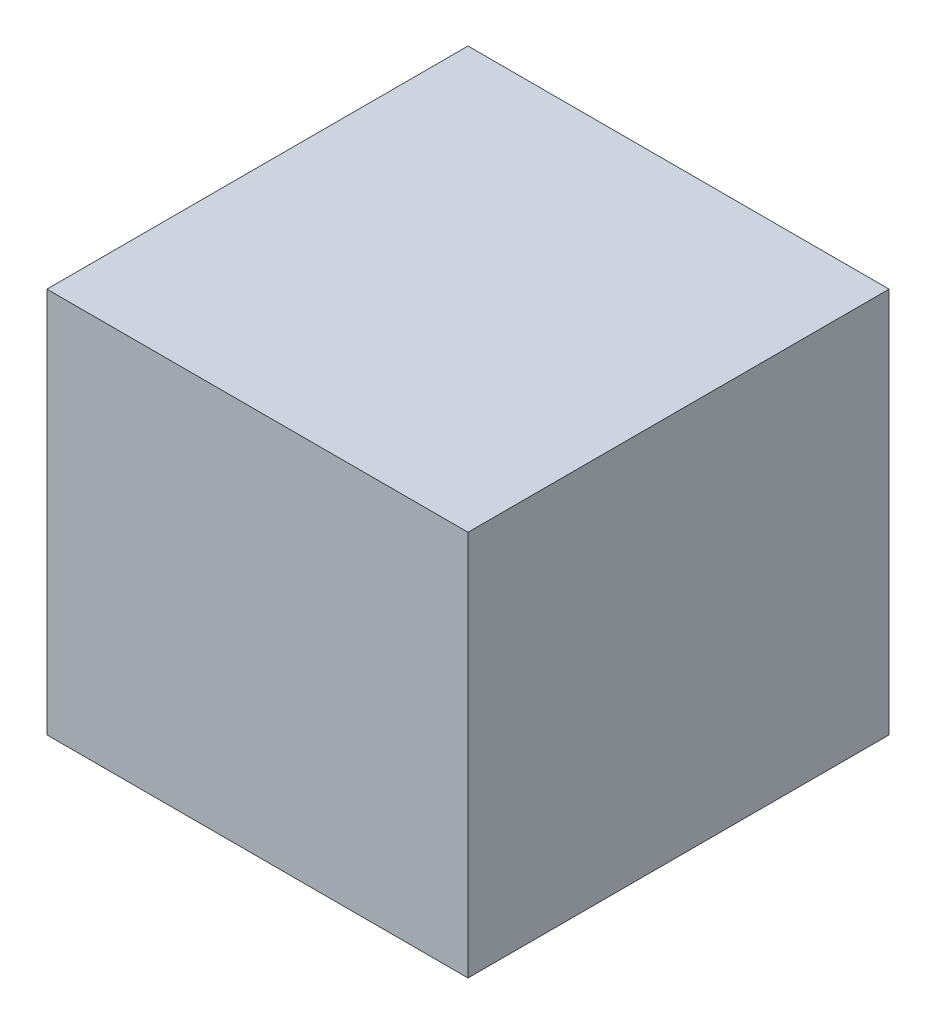
SolidWorks part; units mm, degrees
ref_plane "Front Plane" through (0, 0, 0) normal (0, 0, 1) x (1, 0, 0)
ref_plane "Top Plane" through (0, 0, 0) normal (0, 1, 0) x (1, 0, 0)
ref_plane "Right Plane" through (0, 0, 0) normal (1, 0, 0) x (0, 0, -1)
sketch "Sketch1" plane through (0, 0, 0) normal (0, 0, 1) x (1, 0, 0)
  line L1 (0, 0) -> (304.8, 0)
  line L2 (0, 0) -> (0, 279.4)
  line L3 (0, 279.4) -> (304.8, 279.4)
  line L4 (304.8, 0) -> (304.8, 279.4)
  dimension "D1" = 304.8
  dimension "D2" = 279.4
extrude "Boss-Extrude1" add sketch "Sketch1" along normal blind 304.8
